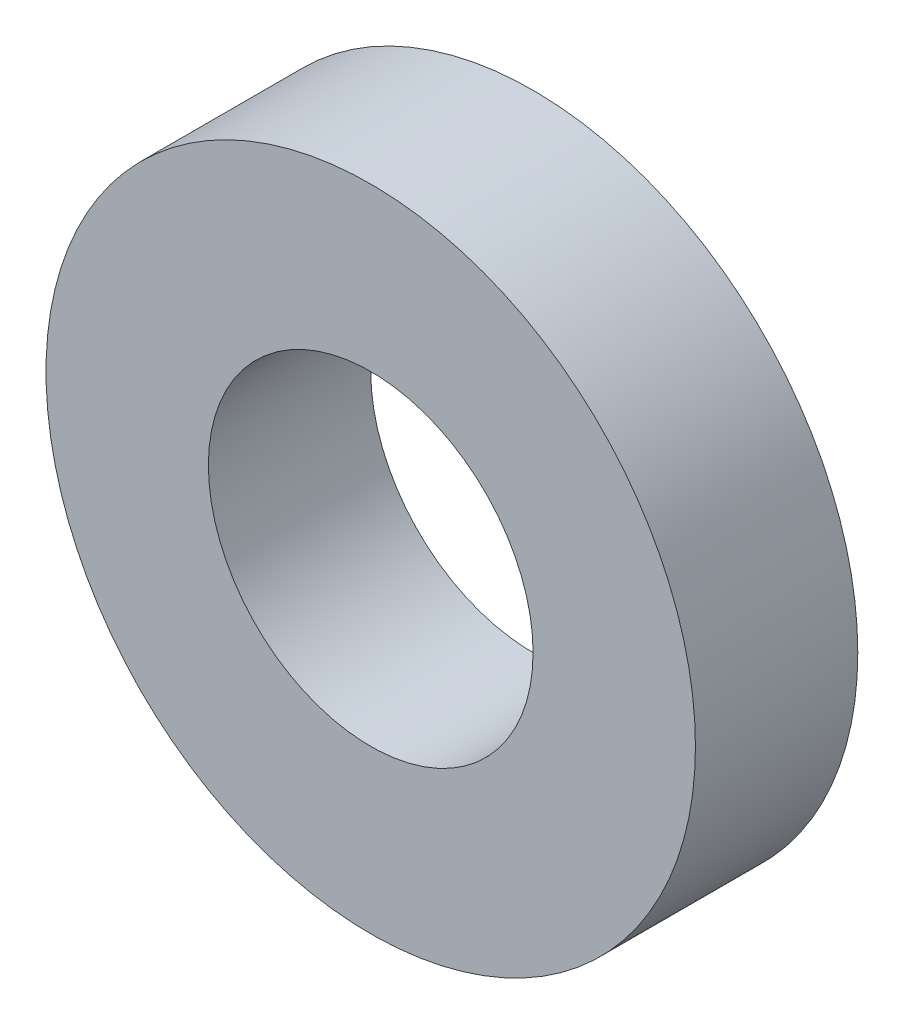
SolidWorks part; units mm, degrees
material "Latón"
ref_plane "Alzado" through (0, 0, 0) normal (0, 0, 1) x (1, 0, 0)
ref_plane "Planta" through (0, 0, 0) normal (0, 1, 0) x (1, 0, 0)
ref_plane "Vista lateral" through (0, 0, 0) normal (1, 0, 0) x (0, 0, -1)
sketch "Croquis1" plane through (0, 0, 0) normal (0, 1, 0) x (1, 0, 0)
  line L0 (0, 0) -> (0, 16.0323) construction
  line L1 (0.5, 0) -> (1, 0)
  line L2 (0.5, 0) -> (0.5, 0.5)
  line L3 (0.5, 0.5) -> (1, 0.5)
  line L4 (1, 0) -> (1, 0.5)
  line L5 (2, 0.5) -> (-2, 0.5) construction
  dimension "D1" = 1
revolve "Revolución1" add sketch "Croquis1" angle 360 about L0
